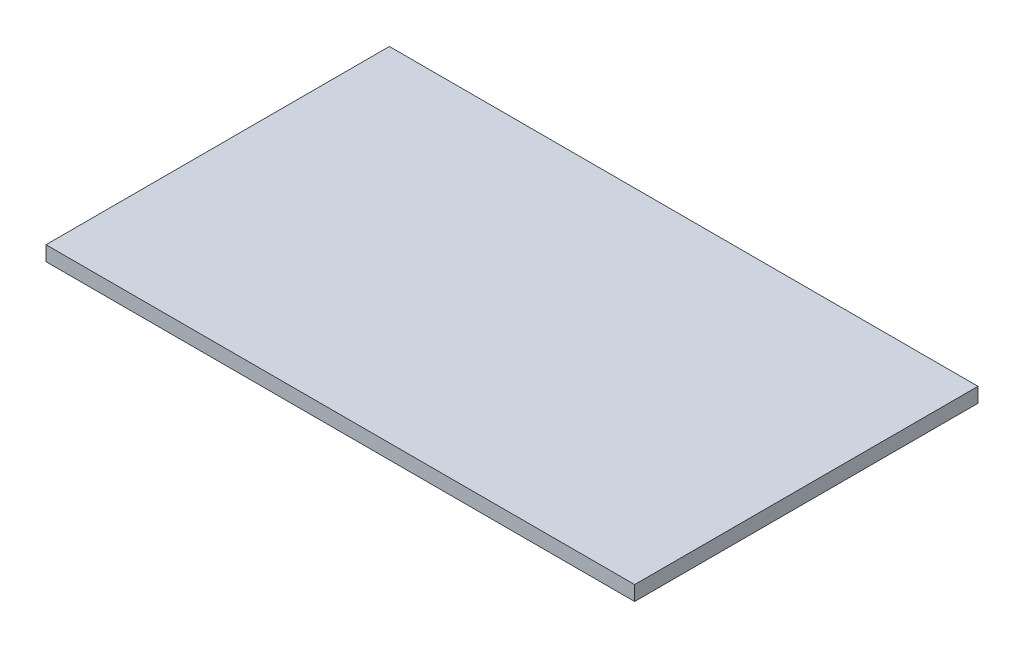
SolidWorks part; units mm, degrees
material "Oak"
ref_plane "Front Plane" through (0, 0, 0) normal (0, 0, 1) x (1, 0, 0)
ref_plane "Top Plane" through (0, 0, 0) normal (0, 1, 0) x (1, 0, 0)
ref_plane "Right Plane" through (0, 0, 0) normal (1, 0, 0) x (0, 0, -1)
sketch "Sketch1" plane through (0, 0, 0) normal (0, 1, 0) x (1, 0, 0)
  line L0 (0, 0) -> (609.6, 0)
  line L1 (609.6, 0) -> (609.6, 355.6)
  line L2 (609.6, 355.6) -> (0, 355.6)
  line L3 (0, 355.6) -> (0, 0)
extrude "Boss-Extrude1" add sketch "Sketch1" along normal blind 15.24
ref_plane "Plane1" through (0, 0, 0) normal (0, -1, 0) x (-1, 0, 0)
